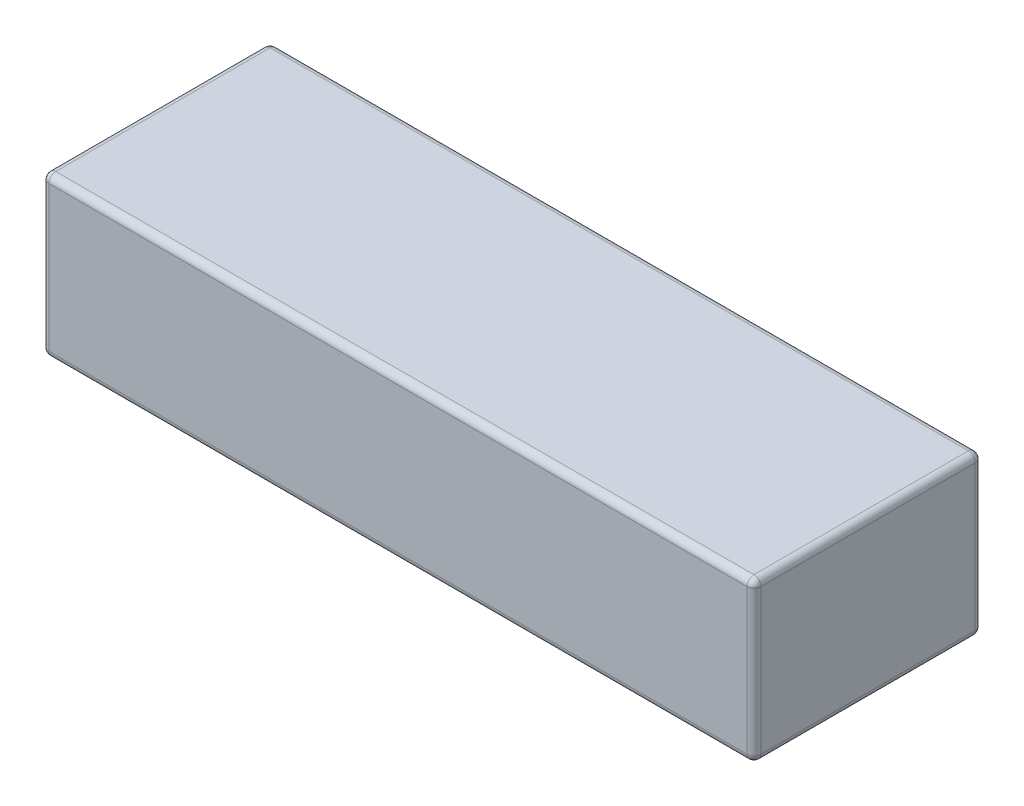
SolidWorks part; units mm, degrees
ref_plane "Front Plane" through (0, 0, 0) normal (0, 0, 1) x (1, 0, 0)
ref_plane "Top Plane" through (0, 0, 0) normal (0, 1, 0) x (1, 0, 0)
ref_plane "Right Plane" through (0, 0, 0) normal (1, 0, 0) x (0, 0, -1)
sketch "Sketch1" plane through (0, 0, 0) normal (1, 0, 0) x (0, 0, -1)
  line L1 (0, 0) -> (33, 0)
  line L2 (0, 0) -> (0, 23)
  line L3 (0, 23) -> (33, 23)
  line L4 (33, 0) -> (33, 23)
  dimension "D1" = 23
  dimension "D2" = 33
extrude "Boss-Extrude1" add sketch "Sketch1" along normal blind 103
fillet "Fillet1" radius 1 12 edges at (0, 11.5, -33) (103, 11.5, -33) (103, 11.5, 0) (0, 11.5, 0) (51.5, 0, 0) (103, 0, -16.5) (51.5, 0, -33) (0, 0, -16.5) (51.5, 23, -33) (103, 23, -16.5) (51.5, 23, 0) (0, 23, -16.5)
